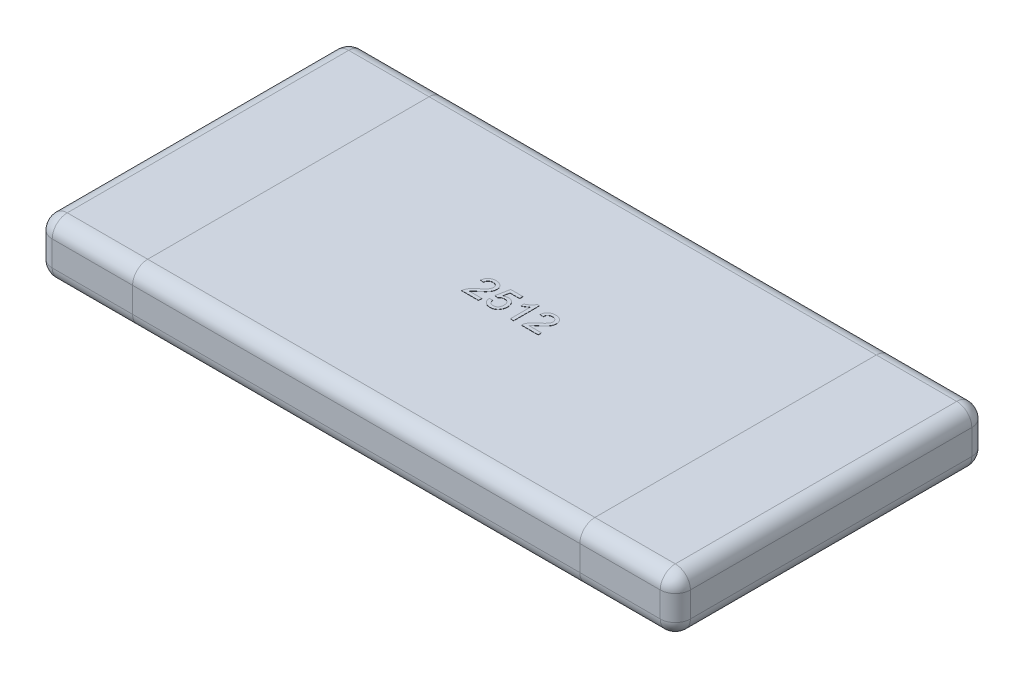
SolidWorks part; units mm, degrees
ref_plane "Front" through (0, 0, 0) normal (0, 0, 1) x (1, 0, 0)
ref_plane "Top" through (0, 0, 0) normal (0, 1, 0) x (1, 0, 0)
ref_plane "Right" through (0, 0, 0) normal (1, 0, 0) x (0, 0, -1)
sketch "Sketch1" plane through (0, 0, 0) normal (0, 1, 0) x (1, 0, 0)
  line L0 (0, -5.3126) -> (0, 5.729) construction
  line L1 (-6.1479, 0) -> (7.7291, 0) construction
  line L3 (-3.175, 1.55) -> (3.175, 1.55)
  line L4 (-3.175, 1.55) -> (-3.175, -1.55)
  line L5 (-3.175, -1.55) -> (3.175, -1.55)
  line L6 (3.175, 1.55) -> (3.175, -1.55)
  dimension "D1" = 6.35
  dimension "D2" = 3.1
extrude "Extrude1" add sketch "Sketch1" along normal blind 0.55
fillet "Fillet1" radius 0.15 12 edges at (0, 0.55, 1.55) (-3.175, 0.275, -1.55) (0, 0, -1.55) (-3.175, 0, 0) (-3.175, 0.275, 1.55) (0, 0, 1.55) (3.175, 0.275, 1.55) (3.175, 0.275, -1.55) (3.175, 0, 0) (0, 0.55, -1.55) (3.175, 0.55, 0) (-3.175, 0.55, 0)
sketch "Sketch2" plane through (0, 0, 1.55) normal (0, 0, 1) x (1, 0, 0)
  line L0 (-3.025, 0.55) -> (3.025, 0.55) construction
  line L1 (-2.225, 0.55) -> (2.225, 0.55)
  line L2 (-2.225, 0.55) -> (-2.225, 0)
  line L3 (-2.225, 0) -> (2.225, 0)
  line L4 (2.225, 0.55) -> (2.225, 0)
  line L5 (3.025, 0) -> (-3.025, 0) construction
  line L6 (-3.175, 0.15) -> (-3.175, 0.4) construction
  line L7 (0, -0.2963) -> (0, 3.0124) construction
  dimension "D1" = 0.95
split line "Split Line1"
sketch "Sketch3" plane through (0, 0.55, 0) normal (0, 1, 0) x (1, 0, 0)
  text T0 "2512" font "Arial" height in points 1
  point P2 (-0.775, 0.2)
  point P3 (-0.775, -0.0317)
  point P4 (0, 0)
  point P5 (0, 0)
  dimension "D1" = 0.4
extrude "Extrude2" add sketch "Sketch3" along normal blind 0.002
